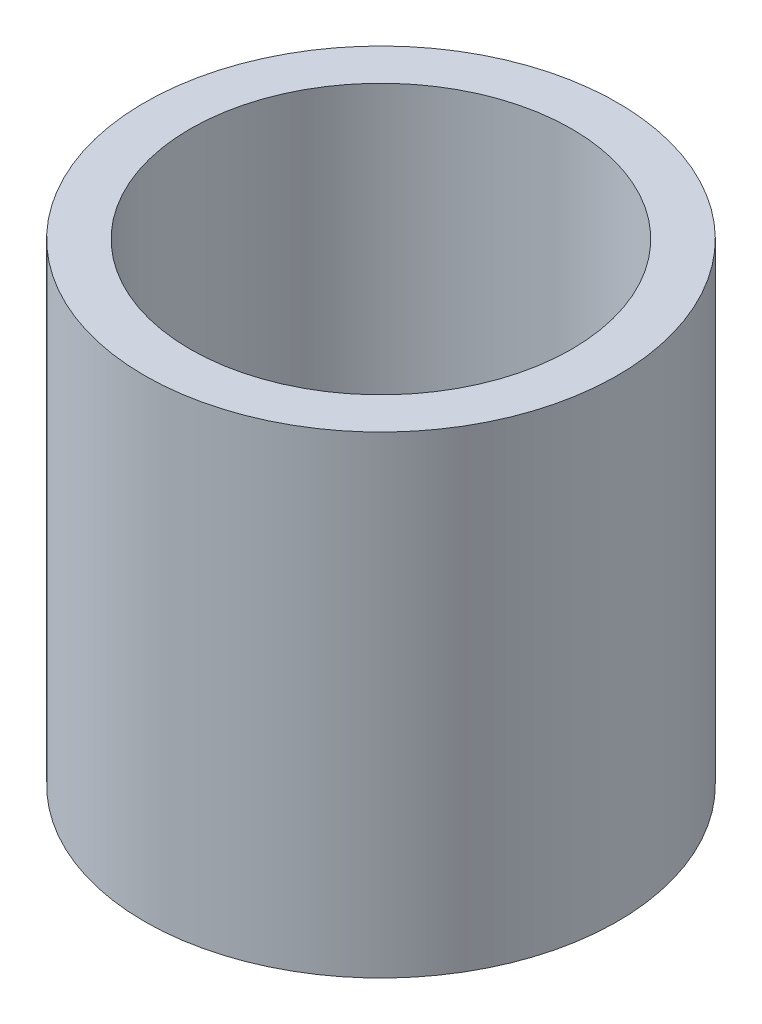
SolidWorks part; units mm, degrees
ref_plane "前视基准面" through (0, 0, 0) normal (0, 0, 1) x (1, 0, 0)
ref_plane "上视基准面" through (0, 0, 0) normal (0, 1, 0) x (1, 0, 0)
ref_plane "右视基准面" through (0, 0, 0) normal (1, 0, 0) x (0, 0, -1)
sketch "草图1" plane through (0, 0, 0) normal (0, 0, 1) x (1, 0, 0)
  line L0 (0, 161.3762) -> (0, 0) construction
  line L1 (141.7365, 0) -> (-131.7984, 0) construction
  line L2 (25.4, 0) -> (25.4, 50.8)
  line L3 (20.5, 50.8) -> (25.4, 50.8)
  line L4 (20.5, 0) -> (25.4, 0)
  line L7 (20.5, 50.8) -> (20.5, 0)
  dimension "D2" = 25.4
  dimension "D3" = 50.8
  dimension "D11" = 20.5
revolve "旋转1" add sketch "草图1" angle 360 about L0
cosmetic thread "装饰螺纹线1" parameters "D2"=42
